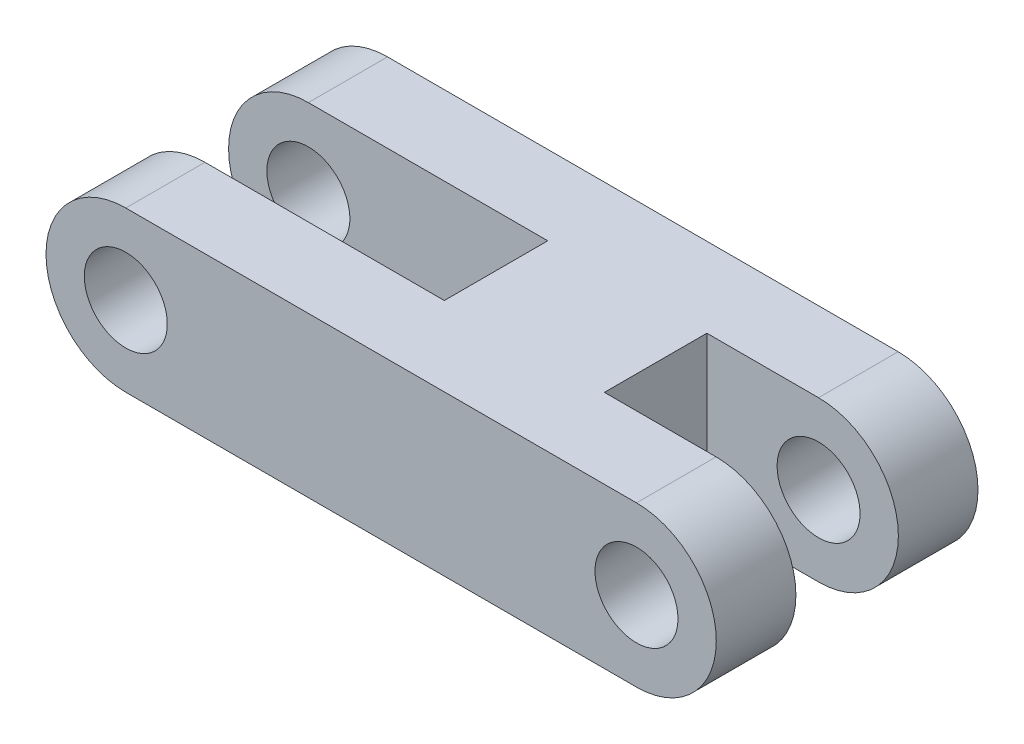
SolidWorks part; units mm, degrees
ref_plane "Front Plane" through (0, 0, 0) normal (0, 0, 1) x (1, 0, 0)
ref_plane "Top Plane" through (0, 0, 0) normal (0, 1, 0) x (1, 0, 0)
ref_plane "Right Plane" through (0, 0, 0) normal (1, 0, 0) x (0, 0, -1)
sketch "Sketch1" plane through (0, 0, 0) normal (0, 0, 1) x (1, 0, 0)
  line L1 (-71.1789, 3.175) -> (-50.8589, 3.175)
  line L2 (-61.0189, 3.175) -> (-61.0189, -2.7618) construction
  line L3 (-71.1789, -3.175) -> (-50.8589, -3.175)
  arc A0 (-50.8589, 3.175) -> (-50.8589, -3.175) centre (-50.8589, 0) cw
  arc A1 (-71.1789, 3.175) -> (-71.1789, -3.175) centre (-71.1789, 0) ccw
  circle A2 centre (-50.8589, 0) radius 1.651
  circle A3 centre (-71.1789, 0) radius 1.651
  dimension "D3" = 3.302
  dimension "D2" = 20.32
extrude "Boss-Extrude1" add sketch "Sketch1" along normal blind 10.414
sketch "Sketch2" plane through (0, 3.175, 0) normal (0, 1, 0) x (1, 0, 0)
  line L0 (-73.8216, -5.207) -> (-38.4144, -5.207) construction
  line L1 (-50.8589, 0) -> (-71.1789, 0) construction
  line L2 (-74.3539, 0) -> (-74.3539, -10.414) construction
  line L3 (-61.6539, -7.2644) -> (-74.3539, -7.2644)
  line L4 (-61.6539, -7.2644) -> (-61.6539, -3.1496)
  line L5 (-61.6539, -3.1496) -> (-74.3539, -3.1496)
  line L6 (-74.3539, -7.2644) -> (-74.3539, -3.1496)
  line L7 (-61.6539, -7.2644) -> (-74.3539, -3.1496) construction
  line L8 (-61.6539, -3.1496) -> (-74.3539, -7.2644) construction
  line L9 (-47.6839, -10.414) -> (-47.6839, 0) construction
  line L10 (-55.3039, -3.1687) -> (-42.6039, -7.2454) construction
  line L11 (-55.3039, -7.2454) -> (-42.6039, -3.1686) construction
  line L12 (-42.6039, -7.2454) -> (-42.6039, -3.1686)
  line L13 (-55.3039, -3.1687) -> (-42.6039, -3.1686)
  line L14 (-55.3039, -7.2454) -> (-55.3039, -3.1687)
  line L15 (-55.3039, -7.2454) -> (-42.6039, -7.2454)
  point P4 (-68.0039, -5.207)
  point P17 (-48.387, -5.207)
  dimension "D1" = 5.207
  dimension "D2" = 4.1148
  dimension "D3" = 12.7
  dimension "D4" = 7.62
extrude "Cut-Extrude1" cut sketch "Sketch2" against normal through all
